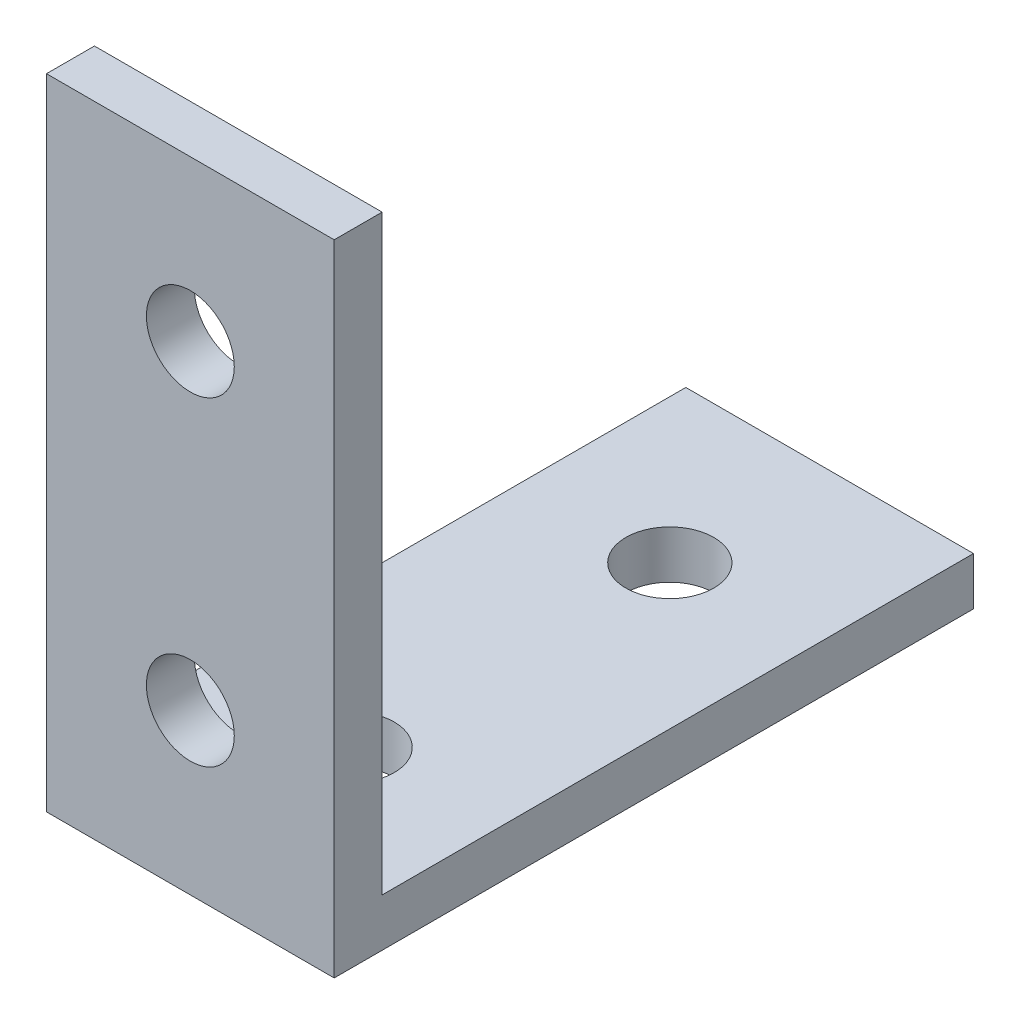
SolidWorks part; units mm, degrees
material "6063-T5"
ref_plane "前视基准面" through (0, 0, 0) normal (0, 0, 1) x (1, 0, 0)
ref_plane "上视基准面" through (0, 0, 0) normal (0, 1, 0) x (1, 0, 0)
ref_plane "右视基准面" through (0, 0, 0) normal (1, 0, 0) x (0, 0, -1)
sketch "草图1" plane through (0, 0, 0) normal (1, 0, 0) x (0, 0, -1)
  line L0 (0, 0) -> (0, -40)
  line L1 (0, -40) -> (40, -40)
  line L2 (40, -40) -> (40, -37)
  line L3 (40, -37) -> (3, -37)
  line L4 (3, -37) -> (3, 0)
  line L5 (3, 0) -> (0, 0)
  dimension "D1" = 40
  dimension "D2" = 40
  dimension "D3" = 3
  dimension "D4" = 3
extrude "凸台-拉伸1" add sketch "草图1" along normal blind 18
sketch "草图3" plane through (0, -40, 0) normal (0, -1, 0) x (1, 0, 0)
  line L0 (9, -10) -> (9, -30) construction
  line L1 (18, 0) -> (0, 0) construction
  line L2 (18, -40) -> (0, -40) construction
  circle A0 centre (9, -10) radius 2.75
  circle A1 centre (9, -30) radius 2.75
  point P3 (9, -20)
  point P5 (9, 0)
  dimension "D3" = 5.5
  dimension "D1" = 10
  dimension "D2" = 20
extrude "切除-拉伸1" cut sketch "草图3" against normal through all both and the other way through all
sketch "草图4" plane through (0, 0, 0) normal (0, 0, 1) x (-1, 0, 0)
  line L0 (-9, 30) -> (-9, 10) construction
  line L3 (-18, 0) -> (0, 0) construction
  circle A0 centre (-9, 30) radius 2.75
  circle A1 centre (-9, 10) radius 2.75
  point P3 (-9, 20)
  point P5 (-9, 0)
  dimension "D3" = 5.5
  dimension "D1" = 10
  dimension "D2" = 20
extrude "切除-拉伸2" cut sketch "草图4" against normal up to next
